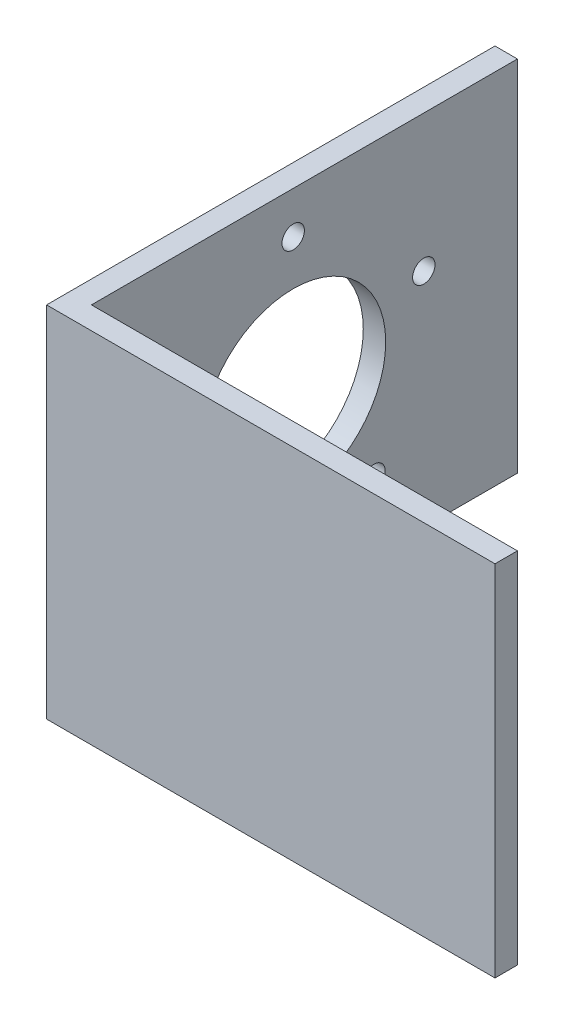
SolidWorks part; units mm, degrees
ref_plane "Front Plane" through (0, 0, 0) normal (0, 0, 1) x (1, 0, 0)
ref_plane "Top Plane" through (0, 0, 0) normal (0, 1, 0) x (1, 0, 0)
ref_plane "Right Plane" through (0, 0, 0) normal (1, 0, 0) x (0, 0, -1)
sketch "Sketch1" plane through (0, 0, 0) normal (0, 1, 0) x (1, 0, 0)
  line L0 (0, 63.5) -> (6.35, 63.5)
  line L1 (6.35, 63.5) -> (6.35, -57.15)
  line L2 (6.35, -57.15) -> (127, -57.15)
  line L3 (127, -57.15) -> (127, -63.5)
  line L4 (127, -63.5) -> (0, -63.5)
  line L5 (0, -63.5) -> (0, 63.5)
  dimension "D1" = 127
  dimension "D2" = 127
  dimension "D3" = 6.35
extrude "Boss-Extrude1" add sketch "Sketch1" along normal mid plane 101.6
sketch "Sketch2" plane through (0, 0, 0) normal (-1, 0, 0) x (0, 0, 1)
  circle A1 centre (0, 0) radius 26.1937
  dimension "D2" = 52.3875
extrude "Cut-Extrude1" cut sketch "Sketch2" against normal through all
sketch "Sketch3" plane through (0, 0, 0) normal (-1, 0, 0) x (0, 0, 1)
  circle A1 centre (0, 38.8938) radius 3.175
  circle A2 centre (0, 0) radius 38.8938
  circle A3 centre (0, 0) radius 38.8938 construction
  dimension "D2" = 6.35
  dimension "D1" = 12.7
extrude "Cut-Extrude2" cut sketch "Sketch3" against normal through all
pattern_circular "CirPattern1" count 5 over 360 about axis through (0, 0, 0) along (1, 0, 0) of "Cut-Extrude2"
